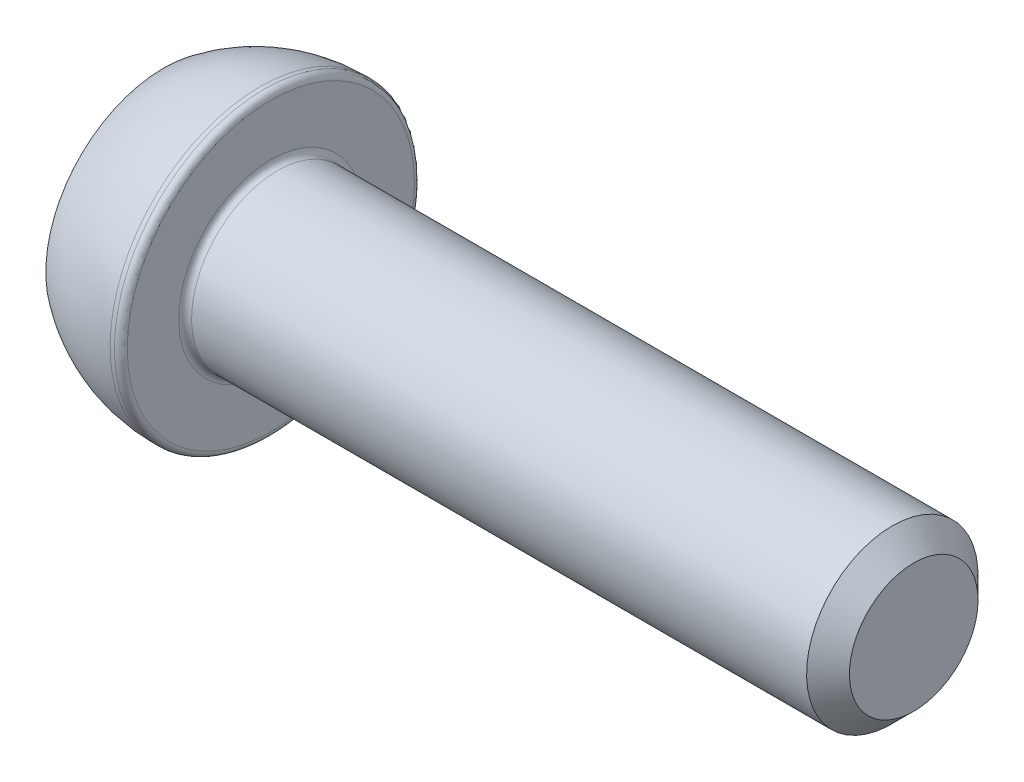
SolidWorks part; units mm, degrees
ref_plane "Спереди" through (0, 0, 0) normal (0, 0, 1) x (1, 0, 0)
ref_plane "Сверху" through (0, 0, 0) normal (0, 1, 0) x (1, 0, 0)
ref_plane "Справа" through (0, 0, 0) normal (1, 0, 0) x (0, 0, -1)
sketch "Эскиз1" plane through (0, 0, 0) normal (0, 0, 1) x (1, 0, 0)
  line L0 (0, 0) -> (0, 5.5)
  line L1 (4.5, 7) -> (5, 7)
  line L2 (5, 7) -> (5, 4)
  line L3 (5, 4) -> (35, 4)
  line L4 (35, 4) -> (35, 0)
  line L5 (35, 0) -> (0, 0) construction
  line L6 (0, 0) -> (35, 0)
  arc A0 (0, 5.5) -> (4.5, 7) centre (4.5, -0.5) cw
  point P9 (5, 5.5)
  dimension "D1" = 0.5
  dimension "D2" = 8
  dimension "D3" = 14
  dimension "D5" = 5
  dimension "D6" = 30
revolve "Повернуть1" add sketch "Эскиз1" angle 360 about L5
cosmetic thread "Условное изображение резьбы1" parameters "D2"=6.619
sketch "Эскиз2" plane through (0, 0, 0) normal (-1, 0, 0) x (0, 0, 1)
  line L1 (1.7321, 3) -> (-1.7321, 3)
  line L2 (-1.7321, 3) -> (-3.4641, 0)
  line L3 (-3.4641, 0) -> (-1.7321, -3)
  line L4 (-1.7321, -3) -> (1.7321, -3)
  line L5 (1.7321, -3) -> (3.4641, 0)
  line L6 (3.4641, 0) -> (1.7321, 3)
  circle A0 centre (0, 0) radius 3 construction
  dimension "D1" = 6
extrude "Вырез-Вытянуть1" cut sketch "Эскиз2" against normal blind 3
fillet "Скругление1" radius 0.3 2 edges at (5, 4, 0) (5, 7, 0)
chamfer "Фаска1" distance 1 angle 45 1 edges at (35, 4, 0)
